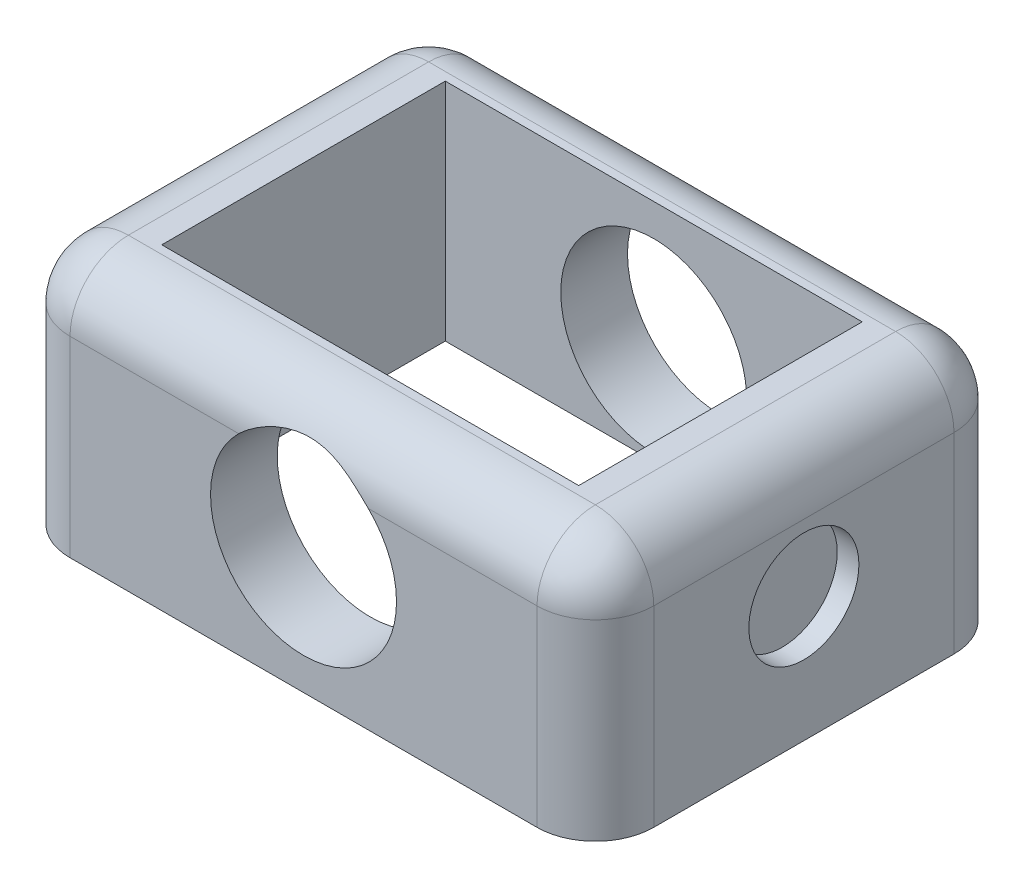
SolidWorks part; units mm, degrees
ref_plane "Front Plane" through (0, 0, 0) normal (0, 0, 1) x (1, 0, 0)
ref_plane "Top Plane" through (0, 0, 0) normal (0, 1, 0) x (1, 0, 0)
ref_plane "Right Plane" through (0, 0, 0) normal (1, 0, 0) x (0, 0, -1)
sketch "Sketch1" plane through (0, 0, 0) normal (0, 1, 0) x (1, 0, 0)
  line L1 (-35, -25) -> (35, -25)
  line L2 (-35, -25) -> (-35, 25)
  line L3 (-35, 25) -> (35, 25)
  line L4 (35, -25) -> (35, 25)
  line L5 (-35, -25) -> (35, 25) construction
  line L6 (-35, 25) -> (35, -25) construction
  point P0 (0, 0)
  dimension "D1" = 70
  dimension "D2" = 50
extrude "Boss-Extrude1" add sketch "Sketch1" along normal mid plane 30
sketch "Sketch2" plane through (0, -15, 0) normal (0, -1, 0) x (1, 0, 0)
  line L0 (-35, 25) -> (35, 25) construction
  line L1 (-25, -17) -> (25, -17)
  line L2 (-25, -17) -> (-25, 17)
  line L3 (-25, 17) -> (25, 17)
  line L4 (25, -17) -> (25, 17)
  line L5 (-25, -17) -> (25, 17) construction
  line L6 (-25, 17) -> (25, -17) construction
  line L7 (-35, -25) -> (-35, 25) construction
  point P0 (0, 0)
  dimension "D1" = 8
  dimension "D2" = 10
extrude "Cut-Extrude1" cut sketch "Sketch2" against normal through all both and the other way through all
fillet "Fillet1" radius 7 8 edges at (-35, 0, 25) (35, 0, 25) (35, 0, -25) (-35, 0, -25) (0, 15, -25) (35, 15, 0) (-35, 15, 0) (0, 15, 25)
chamfer "Chamfer1" distance 3 angle 45 4 edges at (0, -15, -17) (-25, -15, 0) (0, -15, 17) (25, -15, 0)
sketch "Sketch3" plane through (0, 0, -25) normal (0, 0, -1) x (-1, 0, 0)
  circle A0 centre (0, 0) radius 11.15
  dimension "D1" = 22.3
extrude "Cut-Extrude2" cut sketch "Sketch3" against normal through all both and the other way through all
sketch "Sketch4" plane through (35, 0, 0) normal (1, 0, 0) x (0, 0, -1)
  circle A0 centre (0, 0) radius 6.6
  dimension "D1" = 13.2
extrude "Cut-Extrude3" cut sketch "Sketch4" against normal blind 2.6
mirror "Mirror1" about plane through (0, 0, 0) normal (1, 0, 0) of "Cut-Extrude3"
